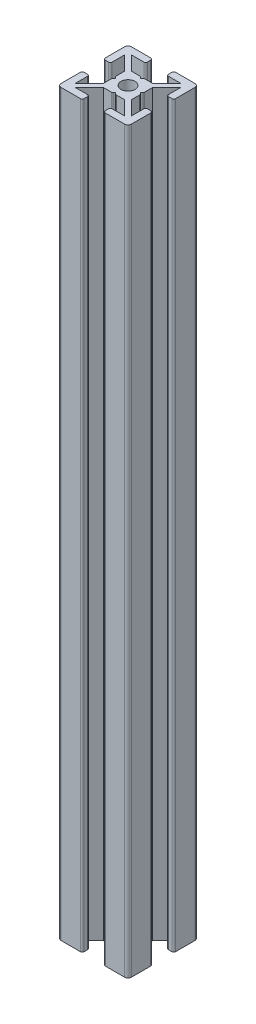
SolidWorks part; units mm, degrees
ref_plane "Front Plane" through (0, 0, 0) normal (0, 0, 1) x (1, 0, 0)
ref_plane "Top Plane" through (0, 0, 0) normal (0, 1, 0) x (1, 0, 0)
ref_plane "Right Plane" through (0, 0, 0) normal (1, 0, 0) x (0, 0, -1)
sketch "Sketch1" plane through (0, 0, 0) normal (0, 1, 0) x (1, 0, 0)
  line L0 (7, 20) -> (7, 18)
  line L1 (0, 0) -> (20, 0)
  line L2 (0, 0) -> (0, 20)
  line L3 (0, 20) -> (20, 20)
  line L4 (20, 0) -> (20, 20)
  line L5 (7, 18) -> (3, 18)
  line L6 (3, 18) -> (7, 14)
  line L7 (7, 14) -> (13, 14)
  line L8 (13, 14) -> (17, 18)
  line L9 (17, 18) -> (13, 18)
  line L10 (13, 18) -> (13, 20)
  line L11 (13, 20) -> (7, 20)
  line L12 (20, 7) -> (20, 13)
  line L13 (20, 13) -> (18, 13)
  line L14 (18, 13) -> (18, 17)
  line L15 (18, 17) -> (14, 13)
  line L16 (14, 13) -> (14, 7)
  line L17 (14, 7) -> (18, 3)
  line L18 (18, 3) -> (18, 7)
  line L19 (18, 7) -> (20, 7)
  line L20 (7, 0) -> (13, 0)
  line L21 (13, 0) -> (13, 2)
  line L22 (13, 2) -> (17, 2)
  line L23 (17, 2) -> (13, 6)
  line L24 (13, 6) -> (7, 6)
  line L25 (7, 6) -> (3, 2)
  line L26 (3, 2) -> (7, 2)
  line L27 (7, 2) -> (7, 0)
  line L28 (0, 13) -> (0, 7)
  line L29 (0, 7) -> (2, 7)
  line L30 (2, 7) -> (2, 3)
  line L31 (2, 3) -> (6, 7)
  line L32 (6, 7) -> (6, 13)
  line L33 (6, 13) -> (2, 17)
  line L34 (2, 17) -> (2, 13)
  line L35 (2, 13) -> (0, 13)
  line L36 (9.5, 14) -> (10.5, 14)
  line L37 (10.5, 14) -> (10, 13.5)
  line L38 (10, 13.5) -> (9.5, 14)
  line L39 (13.5, 10) -> (14, 10.5)
  line L40 (14, 10.5) -> (14, 9.5)
  line L41 (14, 9.5) -> (13.5, 10)
  line L42 (10, 6.5) -> (10.5, 6)
  line L43 (10.5, 6) -> (9.5, 6)
  line L44 (9.5, 6) -> (10, 6.5)
  line L45 (6.5, 10) -> (6, 9.5)
  line L46 (6, 9.5) -> (6, 10.5)
  line L47 (6, 10.5) -> (6.5, 10)
  circle A0 centre (10, 10) radius 2
  point P10 (10, 10)
  point P41 (10, 10)
  point P43 (10, 14)
  point P57 (10, 10)
  dimension "D8" = 4
  dimension "D1" = 20
  dimension "D2" = 20
  dimension "D3" = 7
  dimension "D4" = 7
  dimension "D5" = 6
  dimension "D6" = 4
  dimension "D7" = 4
  dimension "D9" = 0.5
  dimension "D11" = 0.5
  dimension "D12" = 0.5
  dimension "D13" = 4
  dimension "D10" = 4
extrude "Boss-Extrude1" add sketch "Sketch1" along normal blind 210 contours L35 L34 L33 L32 L31 L30 L29 L2 L1 L27 L26 L25 L24 L23 L22 L21 L4 L19 L18 L17 L16 L15 L14 L13 L3 L10 L9 L8 L7 L6 L5 L0 A0
fillet "Fillet1" radius 1 4 edges at (0, 105, -20) (0, 105, 0) (20, 105, 0) (20, 105, -20)
fillet "Fillet2" radius 0.5 16 edges at (20, 105, -13) (18, 105, -13) (20, 105, -7) (18, 105, -7) (13, 105, -2) (13, 105, 0) (7, 105, 0) (7, 105, -2) (0, 105, -7) (2, 105, -7) (13, 105, -20) (13, 105, -18) (7, 105, -20) (7, 105, -18) (0, 105, -13) (2, 105, -13)
fillet "Fillet4" radius 0.5 8 edges at (10.5, 105, -6) (9.5, 105, -6) (6, 105, -9.5) (6, 105, -10.5) (10.5, 105, -14) (9.5, 105, -14) (14, 105, -9.5) (14, 105, -10.5)
